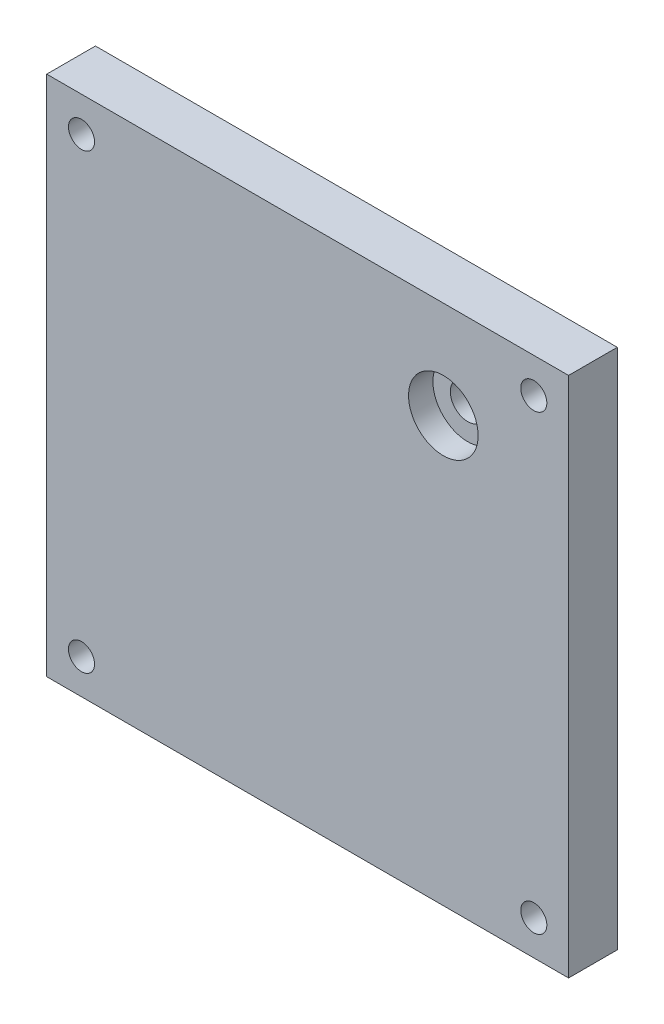
SolidWorks part; units mm, degrees
ref_plane "Front Plane" through (0, 0, 0) normal (0, 0, 1) x (1, 0, 0)
ref_plane "Top Plane" through (0, 0, 0) normal (0, 1, 0) x (1, 0, 0)
ref_plane "Right Plane" through (0, 0, 0) normal (1, 0, 0) x (0, 0, -1)
sketch "Sketch1" plane through (0, 0, 0) normal (0, 0, 1) x (1, 0, 0)
  line L1 (-47.625, -47.625) -> (47.625, -47.625)
  line L2 (-47.625, -47.625) -> (-47.625, 47.625)
  line L3 (-47.625, 47.625) -> (47.625, 47.625)
  line L4 (47.625, -47.625) -> (47.625, 47.625)
  line L5 (-47.625, -47.625) -> (47.625, 47.625) construction
  line L6 (-47.625, 47.625) -> (47.625, -47.625) construction
  point P0 (0, 0)
  dimension "D1" = 95.25
  dimension "D2" = 95.25
extrude "Boss-Extrude1" add sketch "Sketch1" along normal blind 8.89
sketch "Sketch2" plane through (0, 0, 8.89) normal (0, 0, 1) x (1, 0, 0)
  line L0 (47.625, 47.625) -> (-47.625, 47.625) construction
  line L1 (-47.625, -47.625) -> (47.625, -47.625)
  line L2 (-47.625, -47.625) -> (-47.625, 47.625)
  line L3 (-47.625, 47.625) -> (47.625, 47.625)
  line L4 (47.625, -47.625) -> (47.625, 47.625)
  line L5 (-47.625, -47.625) -> (47.625, 47.625) construction
  line L6 (-47.625, 47.625) -> (47.625, -47.625) construction
  line L7 (47.625, -47.625) -> (47.625, 47.625) construction
  line L9 (36.195, -41.275) -> (-36.195, -41.275) construction
  line L10 (41.275, -36.195) -> (41.275, 36.195) construction
  line L11 (36.195, 41.275) -> (-36.195, 41.275) construction
  line L12 (-41.275, -36.195) -> (-41.275, 36.195) construction
  line L13 (41.275, -41.275) -> (-41.275, 41.275) construction
  line L14 (41.275, 41.275) -> (-41.275, -41.275) construction
  arc A0 (-41.275, 36.195) -> (-36.195, 41.275) centre (-41.275, 41.275) ccw construction
  arc A1 (36.195, 41.275) -> (41.275, 36.195) centre (41.275, 41.275) ccw construction
  arc A2 (41.275, -36.195) -> (36.195, -41.275) centre (41.275, -41.275) ccw construction
  arc A3 (-36.195, -41.275) -> (-41.275, -36.195) centre (-41.275, -41.275) ccw construction
  circle A4 centre (-41.275, 41.275) radius 2.3812
  circle A5 centre (41.275, 41.275) radius 2.3812
  circle A6 centre (41.275, -41.275) radius 2.3812
  circle A7 centre (-41.275, -41.275) radius 2.3812
  point P0 (0, 0)
  point P10 (0, 0)
  dimension "D2" = 5.08
  dimension "D3" = 4.7625
  dimension "D1" = 6.35
extrude "Cut-Extrude2" cut sketch "Sketch2" against normal through all flip side to cut
ref_plane "Plane1" through (0, 0, 8.89) normal (0, 0, 1) x (1, 0, 0)
sketch "Sketch3" plane through (0, 0, 8.89) normal (0, 0, 1) x (1, 0, 0)
  line L0 (47.625, -47.625) -> (47.625, 47.625) construction
  line L1 (47.625, 47.625) -> (-47.625, 47.625) construction
  circle A0 centre (24.765, 29.845) radius 6.35
  dimension "D1" = 12.7
  dimension "D2" = 22.86
  dimension "D3" = 17.78
extrude "Cut-Extrude3" cut sketch "Sketch3" against normal blind 4.445 contours A0
sketch "Sketch4" plane through (0, 0, 4.445) normal (0, 0, 1) x (1, 0, 0)
  circle A0 centre (24.765, 29.845) radius 3.175
  dimension "D1" = 6.35
extrude "Cut-Extrude4" cut sketch "Sketch4" against normal through all
